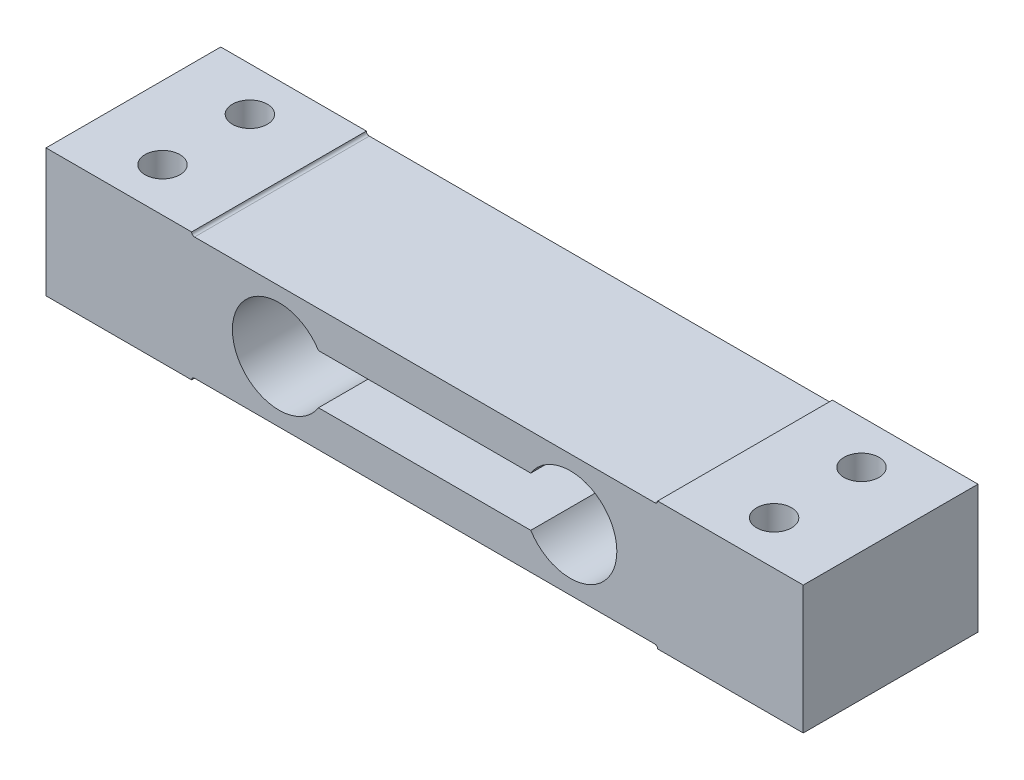
SolidWorks part; units mm, degrees
ref_plane "정면" through (0, 0, 0) normal (0, 0, 1) x (1, 0, 0)
ref_plane "윗면" through (0, 0, 0) normal (0, 1, 0) x (1, 0, 0)
ref_plane "우측면" through (0, 0, 0) normal (1, 0, 0) x (0, 0, -1)
sketch "스케치1" plane through (0, 0, 0) normal (0, 0, 1) x (1, 0, 0)
  line L0 (40, 11) -> (65, 11)
  line L1 (-65, 11) -> (-40, 11)
  line L2 (-65, 11) -> (-65, -11)
  line L3 (-65, -11) -> (-40, -11)
  line L4 (65, 11) -> (65, -11)
  line L5 (-39.5, 10.5) -> (39.5, 10.5)
  line L6 (-39.5, -10.5) -> (39.5, -10.5)
  line L7 (40, -11) -> (65, -11)
  arc A0 (-39.5, -10.5) -> (-40, -11) centre (-39.5, -11) ccw
  arc A1 (-40, 11) -> (-39.5, 10.5) centre (-39.5, 11) ccw
  arc A2 (39.5, 10.5) -> (40, 11) centre (39.5, 11) ccw
  arc A3 (40, -11) -> (39.5, -10.5) centre (39.5, -11) ccw
  point P5 (65, 0)
  point P7 (0, 10.5)
  dimension "D1" = 22
  dimension "D2" = 130
  dimension "D3" = 25
  dimension "D4" = 25
  dimension "D5" = 25
  dimension "D6" = 25
  dimension "D7" = 0.5
extrude "보스-돌출1" add sketch "스케치1" along normal blind 30
sketch "스케치2" plane through (0, 11, 0) normal (0, 1, 0) x (1, 0, 0)
  line L0 (65, 0) -> (40, 0) construction
  line L1 (-40, 0) -> (-65, 0) construction
  circle A0 centre (52.5, -7.5) radius 3
  circle A1 centre (52.5, -22.5) radius 3
  circle A2 centre (-52.5, -7.5) radius 3
  circle A3 centre (-52.5, -22.5) radius 3
  point P15 (52.5, 0)
  point P19 (-52.5, 0)
  dimension "D1" = 6
  dimension "D2" = 15
  dimension "D3" = 7.5
extrude "컷-돌출1" cut sketch "스케치2" against normal up to surface (22 mm away) up to face at (-52.5, -11, 15)
sketch "스케치4" plane through (0, 0, 0) normal (0, 0, -1) x (-1, 0, 0)
  line L1 (-18.2223, 4.25) -> (18.2223, 4.25)
  line L3 (-18.2223, -4.25) -> (18.2223, -4.25)
  arc A0 (-18.2223, 4.25) -> (-18.2223, -4.25) centre (-25, 0) ccw
  arc A1 (18.2223, -4.25) -> (18.2223, 4.25) centre (25, 0) ccw
  point P11 (0, -4.25)
  point P13 (0, 4.25)
  dimension "D1" = 16
  dimension "D2" = 16
  dimension "D3" = 50
  dimension "D4" = 8.5
extrude "컷-돌출2" cut sketch "스케치4" against normal up to surface (30 mm away) contours L1 A1 L3 A0 up to face at (0, 0, 30)
